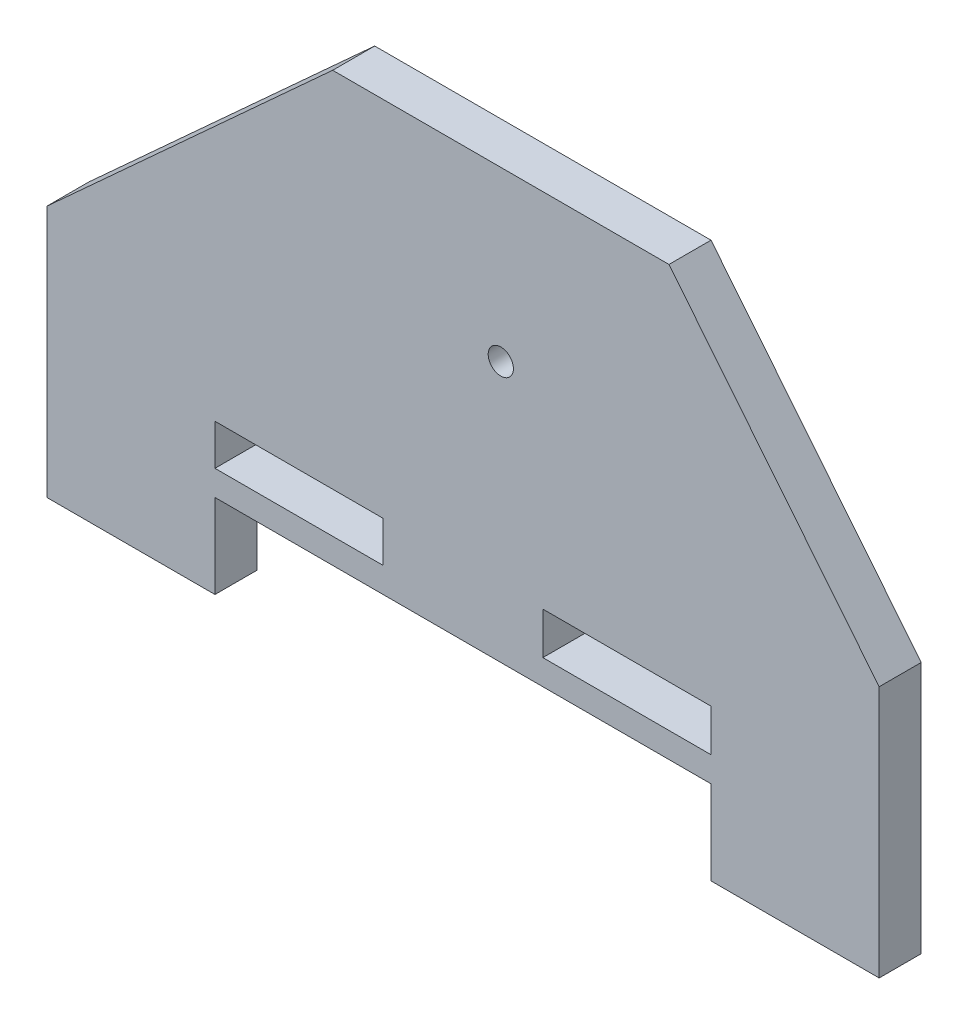
SolidWorks part; units mm, degrees
ref_plane "Front Plane" through (0, 0, 0) normal (0, 0, 1) x (1, 0, 0)
ref_plane "Top Plane" through (0, 0, 0) normal (0, 1, 0) x (1, 0, 0)
ref_plane "Right Plane" through (0, 0, 0) normal (1, 0, 0) x (0, 0, -1)
sketch "Sketch1" plane through (0, 0, 0) normal (0, 0, 1) x (1, 0, 0)
  line L0 (-36.4824, -14.4861) -> (-16.4824, -14.4861)
  line L1 (-16.4824, -14.4861) -> (-16.4824, -4.4861)
  line L2 (-16.4824, -4.4861) -> (42.5176, -4.4861)
  line L3 (42.5176, -4.4861) -> (42.5176, -14.4861)
  line L4 (42.5176, -14.4861) -> (62.5176, -14.4861)
  line L5 (62.5176, -14.4861) -> (62.5176, 15.5139)
  line L6 (-36.4824, -14.4861) -> (-36.4824, 15.5139)
  line L7 (17.5176, -4.4861) -> (17.5176, 26.5139) construction
  line L8 (17.5176, 26.5139) -> (17.5176, 46.5139) construction
  line L9 (-16.4824, -1.4861) -> (3.5176, -1.4861)
  line L10 (-16.4824, -1.4861) -> (-16.4824, 3.3626)
  line L11 (-16.4824, 3.3626) -> (3.5176, 3.3626)
  line L12 (3.5176, -1.4861) -> (3.5176, 3.3626)
  line L13 (22.5176, -1.4861) -> (42.5176, -1.4861)
  line L14 (22.5176, -1.4861) -> (22.5176, 3.5139)
  line L15 (22.5176, 3.5139) -> (42.5176, 3.5139)
  line L16 (42.5176, -1.4861) -> (42.5176, 3.5139)
  line L17 (17.5176, 46.5139) -> (-2.4824, 46.5139)
  line L18 (17.5176, 46.5139) -> (37.5176, 46.5139)
  line L19 (-36.4824, 15.5139) -> (-2.4824, 46.5139)
  line L20 (37.5176, 46.5139) -> (62.5176, 15.5139)
  circle A0 centre (17.5176, 26.5139) radius 1.5
  point P19 (42.5176, 1.0139)
  dimension "D10" = 3
  dimension "D1" = 30
  dimension "D2" = 30
  dimension "D3" = 20
  dimension "D4" = 59
  dimension "D5" = 20
  dimension "D6" = 10
  dimension "D7" = 10
  dimension "D8" = 34
  dimension "D9" = 31
  dimension "D11" = 20
  dimension "D12" = 20
  dimension "D13" = 0
  dimension "D14" = 3
  dimension "D15" = 3
  dimension "D16" = 20
  dimension "D17" = 20
  dimension "D18" = 20
  dimension "D19" = 5
extrude "Boss-Extrude1" add sketch "Sketch1" along normal blind 5
